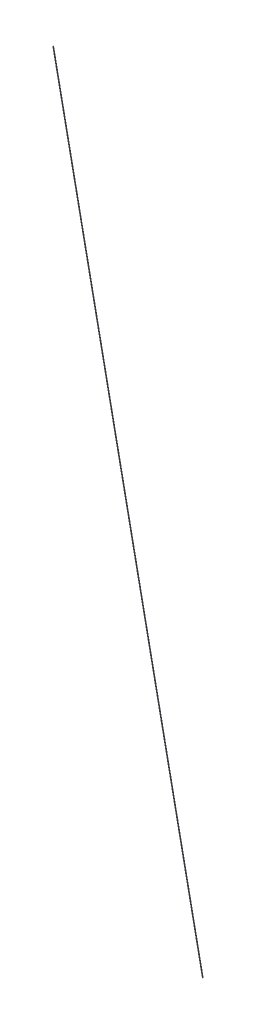
SolidWorks part; units mm, degrees
ref_plane "前视基准面" through (0, 0, 0) normal (0, 0, 1) x (1, 0, 0)
ref_plane "上视基准面" through (0, 0, 0) normal (0, 1, 0) x (1, 0, 0)
ref_plane "右视基准面" through (0, 0, 0) normal (1, 0, 0) x (0, 0, -1)
sketch "草图2" plane through (0, 0, 0) normal (0, 0, 1) x (1, 0, 0)
  line L5 (307.5, 0) -> (0, 1505)
sweep "扫描2" add path "草图2" circular profile diameter 1 parameters "D3"=1
